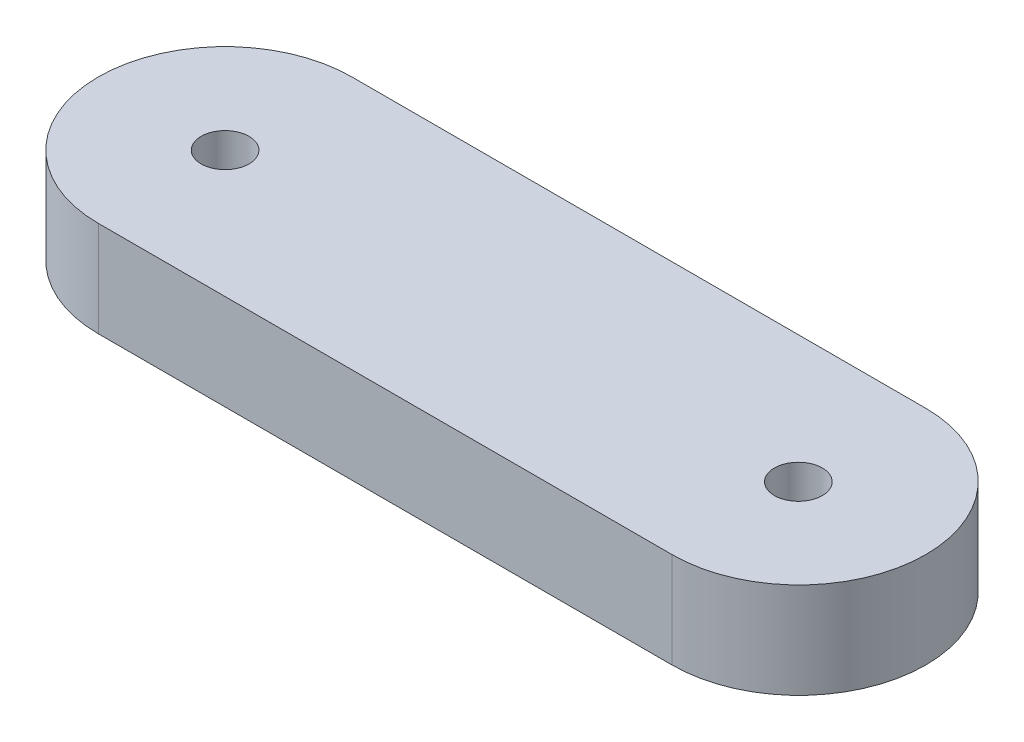
SolidWorks part; units mm, degrees
ref_plane "Спереди" through (0, 0, 0) normal (0, 0, 1) x (1, 0, 0)
ref_plane "Сверху" through (0, 0, 0) normal (0, 1, 0) x (1, 0, 0)
ref_plane "Справа" through (0, 0, 0) normal (1, 0, 0) x (0, 0, -1)
sketch "Эскиз1" plane through (0, 0, 0) normal (0, 1, 0) x (1, 0, 0)
  line L0 (-16.4089, 1.8552) -> (19.5911, 1.8549)
  line L1 (-16.4089, -14.0535) -> (19.5911, -14.0535)
  line L2 (-16.4089, 1.8552) -> (-16.4089, -14.0535) construction
  circle A0 centre (19.5911, -6.1355) radius 1.5019
  arc A1 (-16.4089, 1.8552) -> (-16.4089, -14.0535) centre (-16.4089, -6.0991) ccw
  circle A2 centre (-16.4089, -6.0991) radius 1.5019
  arc A3 (19.5911, -14.0535) -> (19.5911, 1.8549) centre (19.5911, -6.0993) ccw
  dimension "D1" = 36
  dimension "D2" = 36
  dimension "D3" = 36
extrude "Бобышка-Вытянуть1" add sketch "Эскиз1" along normal blind 6
